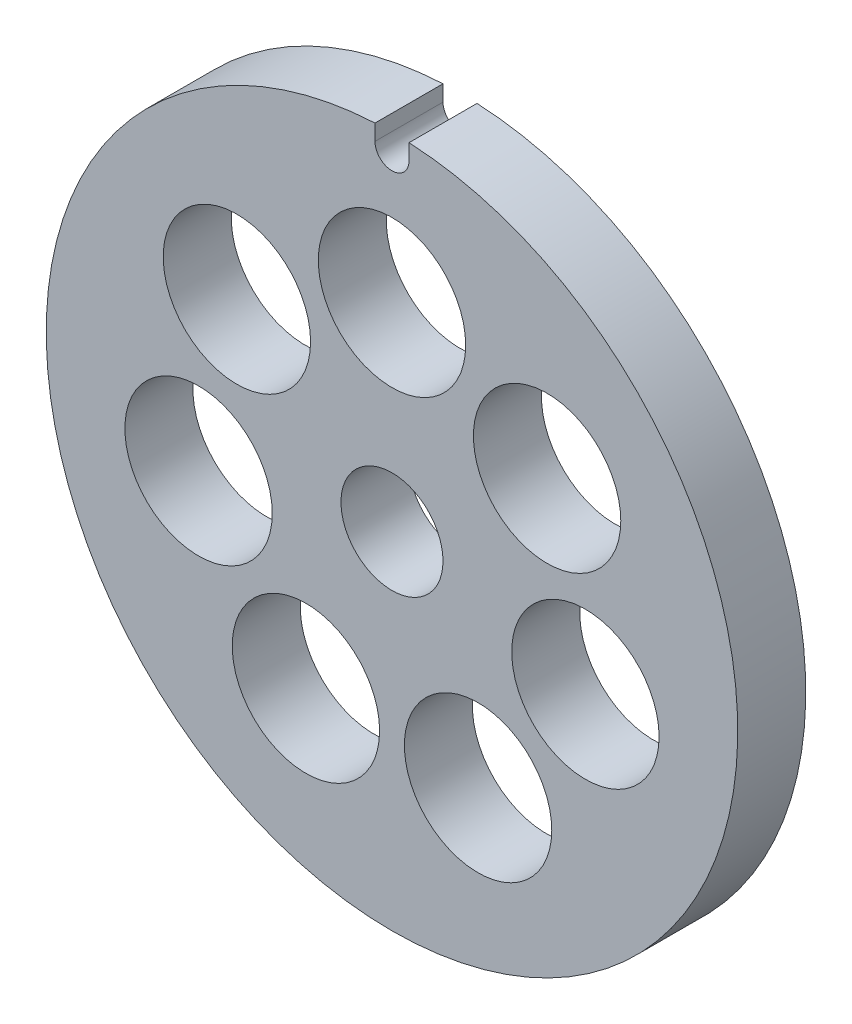
SolidWorks part; units mm, degrees
ref_plane "Front Plane" through (0, 0, 0) normal (0, 0, 1) x (1, 0, 0)
ref_plane "Top Plane" through (0, 0, 0) normal (0, 1, 0) x (1, 0, 0)
ref_plane "Right Plane" through (0, 0, 0) normal (1, 0, 0) x (0, 0, -1)
sketch "Sketch1" plane through (0, 0, 0) normal (0, 0, 1) x (1, 0, 0)
  line L0 (-1.5, 29.0631) -> (-1.5, 30.4631)
  line L1 (1.5, 29.0631) -> (1.5, 30.4631)
  arc A0 (-1.5, 30.4631) -> (1.5, 30.4631) centre (0, 0) ccw
  circle A1 centre (0, 0) radius 4.5
  circle A2 centre (0, 17.5) radius 6.5
  arc A3 (-1.5, 29.0631) -> (1.5, 29.0631) centre (0, 29.0631) ccw
  circle A4 centre (13.6821, 10.9111) radius 6.5
  circle A5 centre (17.0612, -3.8941) radius 6.5
  circle A6 centre (7.593, -15.767) radius 6.5
  circle A7 centre (-7.593, -15.767) radius 6.5
  circle A8 centre (-17.0612, -3.8941) radius 6.5
  circle A9 centre (-13.6821, 10.9111) radius 6.5
  point P1 (29.656, -2.5611)
  point P7 (0, 0)
  point P25 (0, 0)
  dimension "D1" = 61
  dimension "D2" = 13
  dimension "D3" = 9
  dimension "D4" = 3
  dimension "D5" = 1.4
  dimension "D6" = 1.4
  dimension "D7" = 17.5
  dimension "D8" = 7
extrude "Boss-Extrude1" add sketch "Sketch1" along normal blind 6
